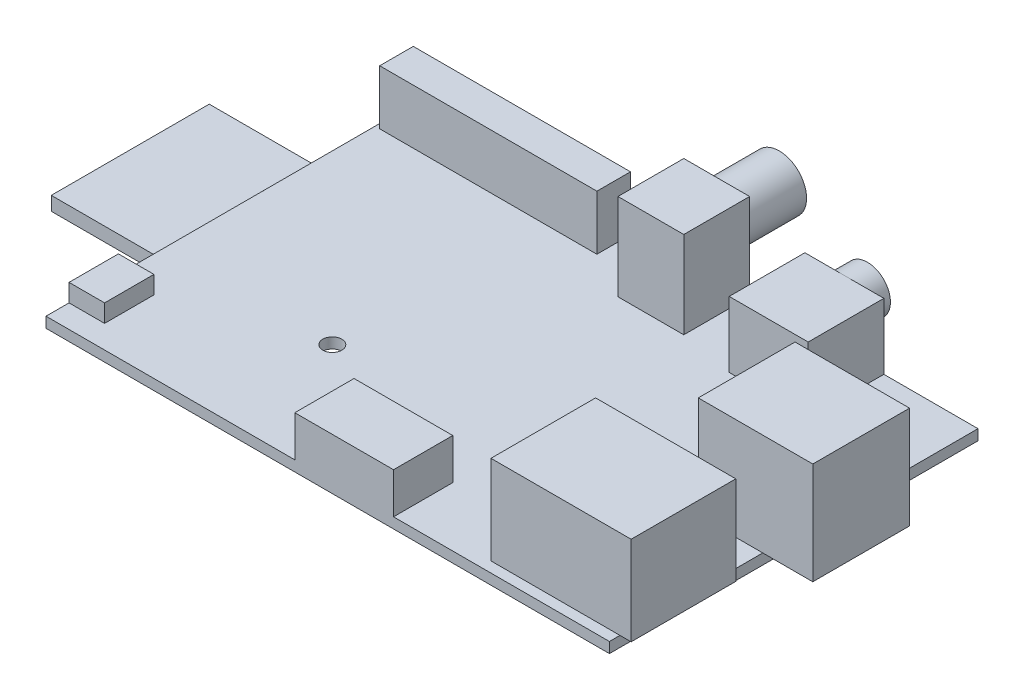
SolidWorks part; units mm, degrees
ref_plane "Front Plane" through (0, 0, 0) normal (0, 0, 1) x (1, 0, 0)
ref_plane "Top Plane" through (0, 0, 0) normal (0, 1, 0) x (1, 0, 0)
ref_plane "Right Plane" through (0, 0, 0) normal (1, 0, 0) x (0, 0, -1)
sketch "Sketch1" plane through (0, 0, 0) normal (0, 1, 0) x (1, 0, 0)
  line L1 (42.8, 28) -> (-42.8, 28)
  line L2 (42.8, 28) -> (42.8, -28)
  line L3 (42.8, -28) -> (-42.8, -28)
  line L4 (-42.8, 28) -> (-42.8, -28)
  line L5 (42.8, 28) -> (-42.8, -28) construction
  line L6 (42.8, -28) -> (-42.8, 28) construction
  point P0 (0, 0)
  dimension "D1" = 85.6
  dimension "D2" = 56
extrude "Boss-Extrude1" add sketch "Sketch1" along normal blind 1.6
sketch "Sketch2" plane through (0, 1.6, 0) normal (0, 1, 0) x (1, 0, 0)
  line L0 (-42.8, -28) -> (42.8, -28) construction
  line L1 (23.2, -10.5) -> (44.5, -10.5)
  line L2 (23.2, -10.5) -> (23.2, -26.4)
  line L3 (23.2, -26.4) -> (44.5, -26.4)
  line L4 (44.5, -10.5) -> (44.5, -26.4)
  line L5 (23.2, -10.5) -> (44.5, -26.4) construction
  line L6 (23.2, -26.4) -> (44.5, -10.5) construction
  line L7 (42.8, -28) -> (42.8, 28) construction
  point P0 (33.85, -18.45)
  dimension "D1" = 21.3
  dimension "D2" = 15.9
  dimension "D3" = 1.6
  dimension "D4" = 1.7
extrude "Boss-Extrude2" add sketch "Sketch2" along normal blind 13.5
sketch "Sketch3" plane through (0, 1.6, 0) normal (0, 1, 0) x (1, 0, 0)
  line L0 (42.8, 28) -> (-42.8, 28) construction
  line L1 (33, 10) -> (50.4, 10)
  line L2 (33, 10) -> (33, -4.7)
  line L3 (33, -4.7) -> (50.4, -4.7)
  line L4 (50.4, 10) -> (50.4, -4.7)
  line L5 (33, 10) -> (50.4, -4.7) construction
  line L6 (33, -4.7) -> (50.4, 10) construction
  line L7 (42.8, -10.5) -> (42.8, 28) construction
  point P0 (41.7, 2.65)
  dimension "D1" = 14.7
  dimension "D2" = 17.4
  dimension "D3" = 18
  dimension "D4" = 7.6
extrude "Boss-Extrude3" add sketch "Sketch3" along normal blind 15.5
sketch "Sketch4" plane through (0, 0, 0) normal (0, -1, 0) x (1, 0, 0)
  line L0 (-42.8, -28) -> (-42.8, 28) construction
  line L1 (-42.8, -15.9) -> (-26, -15.9)
  line L2 (-42.8, -15.9) -> (-42.8, 12.9)
  line L3 (-42.8, 12.9) -> (-26, 12.9)
  line L4 (-26, -15.9) -> (-26, 12.9)
  line L6 (42.8, -28) -> (-42.8, -28) construction
  dimension "D1" = 28.8
  dimension "D2" = 16.8
  dimension "D3" = 12.1
extrude "Boss-Extrude4" add sketch "Sketch4" along normal blind 3.4
sketch "Sketch5" plane through (-42.8, 0, 0) normal (-1, 0, 0) x (0, 0, 1)
  line L0 (-28, 1.6) -> (-28, 0) construction
  line L1 (-14.5, -0.6) -> (9.5, -0.6)
  line L2 (-14.5, -0.6) -> (-14.5, -2.7)
  line L3 (-14.5, -2.7) -> (9.5, -2.7)
  line L4 (9.5, -0.6) -> (9.5, -2.7)
  line L5 (12.9, -3.4) -> (-15.9, -3.4) construction
  dimension "D1" = 24
  dimension "D2" = 13.5
  dimension "D3" = 0.7
  dimension "D4" = 2.1
extrude "Boss-Extrude5" add sketch "Sketch5" along normal blind 17.7
sketch "Sketch6" plane through (0, 1.6, 0) normal (0, 1, 0) x (1, 0, 0)
  line L0 (42.8, 28) -> (-42.8, 28) construction
  line L1 (-1.9, 28) -> (8.1, 28)
  line L2 (-1.9, 28) -> (-1.9, 18)
  line L3 (-1.9, 18) -> (8.1, 18)
  line L4 (8.1, 28) -> (8.1, 18)
  line L5 (-1.9, 28) -> (8.1, 18) construction
  line L6 (-1.9, 18) -> (8.1, 28) construction
  line L7 (42.8, 10) -> (42.8, 28) construction
  point P0 (3.1, 23)
  dimension "D1" = 10
  dimension "D2" = 10
  dimension "D3" = 34.7
extrude "Boss-Extrude6" add sketch "Sketch6" along normal blind 13.2
sketch "Sketch7" plane through (0, 0, -28) normal (0, 0, -1) x (-1, 0, 0)
  line L0 (-3.1, 14.8) -> (-3.1, -49985.2) construction
  line L1 (-8.1, 14.8) -> (1.9, 14.8) construction
  circle A0 centre (-3.1, 9.4) radius 4.15
  point P4 (-3.1, 14.8)
  dimension "D1" = 5.4
  dimension "D2" = 8.3
extrude "Boss-Extrude7" add sketch "Sketch7" along normal blind 9.5
sketch "Sketch8" plane through (0, 1.6, 0) normal (0, 1, 0) x (1, 0, 0)
  line L0 (42.8, 28) -> (8.1, 28) construction
  line L1 (16.5, 16.5) -> (28.5, 16.5)
  line L2 (16.5, 16.5) -> (16.5, 28)
  line L3 (16.5, 28) -> (28.5, 28)
  line L4 (28.5, 16.5) -> (28.5, 28)
  line L5 (16.5, 16.5) -> (28.5, 28) construction
  line L6 (16.5, 28) -> (28.5, 16.5) construction
  line L7 (42.8, 10) -> (42.8, 28) construction
  point P0 (22.5, 22.25)
  dimension "D1" = 12
  dimension "D2" = 11.5
  dimension "D3" = 14.3
extrude "Boss-Extrude8" add sketch "Sketch8" along normal blind 10
sketch "Sketch9" plane through (0, 0, -28) normal (0, 0, -1) x (-1, 0, 0)
  line L0 (-22.5, 11.6) -> (-22.5, -49988.4) construction
  line L1 (-28.5, 11.6) -> (-16.5, 11.6) construction
  circle A0 centre (-22.5, 8.1) radius 3.5
  point P6 (-22.5, 11.6)
  dimension "D1" = 7
extrude "Boss-Extrude9" add sketch "Sketch9" along normal blind 3.5
sketch "Sketch10" plane through (0, 1.6, 0) normal (0, 1, 0) x (1, 0, 0)
  line L0 (-42.8, 28) -> (-42.8, -28) construction
  line L1 (-42.1, 27.1) -> (-9.1, 27.1)
  line L2 (-42.1, 27.1) -> (-42.1, 22)
  line L3 (-42.1, 22) -> (-9.1, 22)
  line L4 (-9.1, 27.1) -> (-9.1, 22)
  line L5 (-42.1, 27.1) -> (-9.1, 22) construction
  line L6 (-42.1, 22) -> (-9.1, 27.1) construction
  line L7 (-1.9, 28) -> (-42.8, 28) construction
  point P0 (-25.6, 24.55)
  dimension "D1" = 33
  dimension "D2" = 5.1
  dimension "D3" = 0.7
  dimension "D4" = 0.9
extrude "Boss-Extrude10" add sketch "Sketch10" along normal blind 8.3
sketch "Sketch11" plane through (0, 1.6, 0) normal (0, 1, 0) x (1, 0, 0)
  line L0 (-42.8, 28) -> (-42.8, -28) construction
  line L1 (-37.4, -17) -> (-42.8, -17)
  line L2 (-37.4, -17) -> (-37.4, -24.5)
  line L3 (-37.4, -24.5) -> (-42.8, -24.5)
  line L4 (-42.8, -17) -> (-42.8, -24.5)
  line L5 (-42.8, -28) -> (42.8, -28) construction
  dimension "D1" = 7.5
  dimension "D2" = 5.4
  dimension "D3" = 3.5
extrude "Boss-Extrude11" add sketch "Sketch11" along normal blind 2.7
sketch "Sketch12" plane through (0, 1.6, 0) normal (0, 1, 0) x (1, 0, 0)
  line L0 (-42.8, -28) -> (42.8, -28) construction
  line L1 (-5, -28) -> (10, -28)
  line L2 (-5, -28) -> (-5, -19)
  line L3 (-5, -19) -> (10, -19)
  line L4 (10, -28) -> (10, -19)
  line L5 (42.8, -28) -> (42.8, -26.4) construction
  dimension "D1" = 15
  dimension "D2" = 9
  dimension "D3" = 32.8
extrude "Boss-Extrude12" add sketch "Sketch12" along normal blind 6.2
sketch "Sketch13" plane through (0, 1.6, 0) normal (0, 1, 0) x (1, 0, 0)
  line L0 (-42.8, 28) -> (-42.8, -17) construction
  line L1 (-42.8, -28) -> (-5, -28) construction
  line L2 (42.8, 10) -> (42.8, 28) construction
  line L3 (42.8, 28) -> (28.5, 28) construction
  circle A0 centre (-17.3, -10) radius 1.45
  circle A1 centre (37.8, 15.5) radius 1.45
  dimension "D5" = 2.9
  dimension "D1" = 25.5
  dimension "D2" = 18
  dimension "D3" = 5
  dimension "D4" = 12.5
extrude "Cut-Extrude1" cut sketch "Sketch13" against normal through all
